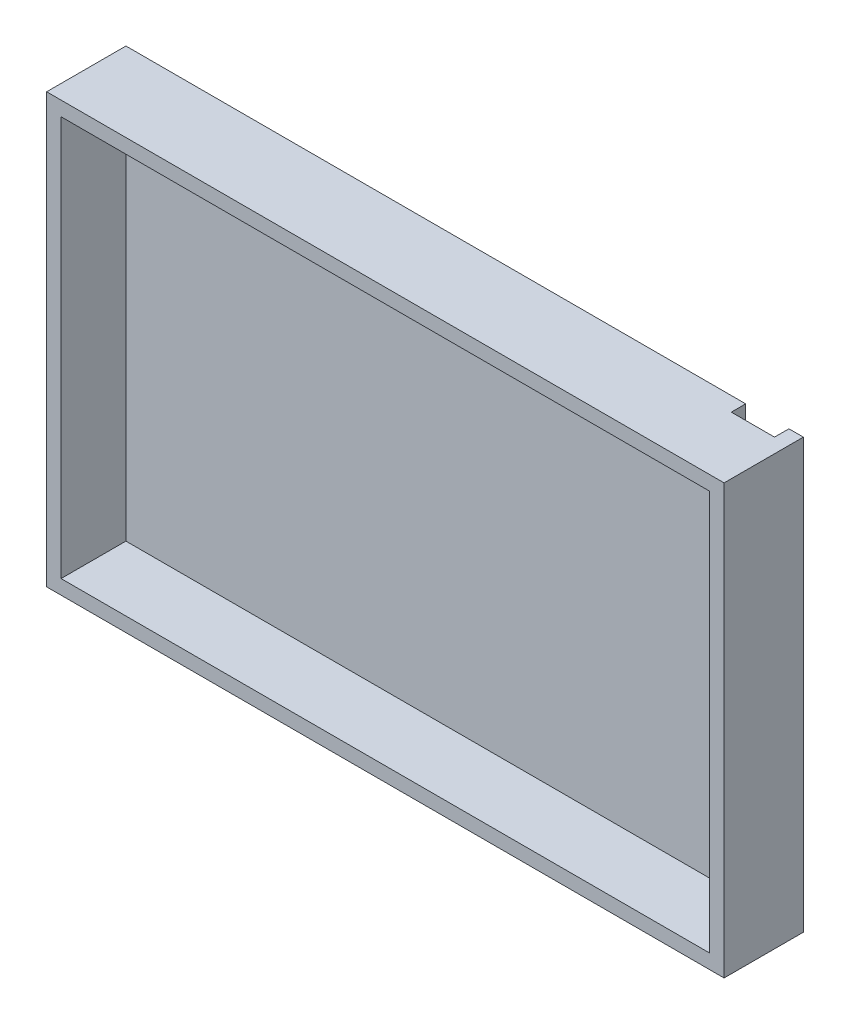
SolidWorks part; units mm, degrees
ref_plane "Front Plane" through (0, 0, 0) normal (0, 0, 1) x (1, 0, 0)
ref_plane "Top Plane" through (0, 0, 0) normal (0, 1, 0) x (1, 0, 0)
ref_plane "Right Plane" through (0, 0, 0) normal (1, 0, 0) x (0, 0, -1)
sketch "Sketch2" plane through (0, 0, 0) normal (0, 0, 1) x (1, 0, 0)
  line L1 (-47, 29.75) -> (47, 29.75)
  line L2 (-47, 29.75) -> (-47, -29.75)
  line L3 (-47, -29.75) -> (47, -29.75)
  line L4 (47, 29.75) -> (47, -29.75)
  line L5 (-47, 29.75) -> (47, -29.75) construction
  line L6 (-47, -29.75) -> (47, 29.75) construction
  point P0 (0, 0)
  dimension "D1" = 94
  dimension "D2" = 59.5
extrude "Boss-Extrude1" add sketch "Sketch2" along normal blind 11
sketch "Sketch3" plane through (0, 0, 11) normal (0, 0, 1) x (1, 0, 0)
  line L1 (-45, 27.75) -> (45, 27.75)
  line L2 (-45, 27.75) -> (-45, -27.75)
  line L3 (-45, -27.75) -> (45, -27.75)
  line L4 (45, 27.75) -> (45, -27.75)
  line L5 (-45, 27.75) -> (45, -27.75) construction
  line L6 (-45, -27.75) -> (45, 27.75) construction
  point P0 (0, 0)
  dimension "D1" = 90
  dimension "D2" = 55.5
extrude "Cut-Extrude1" cut sketch "Sketch3" against normal blind 9
sketch "Sketch5" plane through (0, 0, 0) normal (0, 0, -1) x (-1, 0, 0)
  line L1 (-47, 29.75) -> (47, 29.75) construction
  line L2 (-45, 29.75) -> (-45, -29.75)
  line L3 (47, -29.75) -> (-47, -29.75) construction
  line L6 (-45, 29.75) -> (-39, 29.75)
  line L8 (-45, -29.75) -> (-39, -29.75)
  line L9 (-39, 29.75) -> (-39, -29.75)
  line L10 (-45, 29.75) -> (-39, -29.75) construction
  line L11 (-45, -29.75) -> (-39, 29.75) construction
  point P11 (-42, 0)
  dimension "D1" = 59.5
  dimension "D2" = 6
extrude "Cut-Extrude2" cut sketch "Sketch5" against normal blind 2
